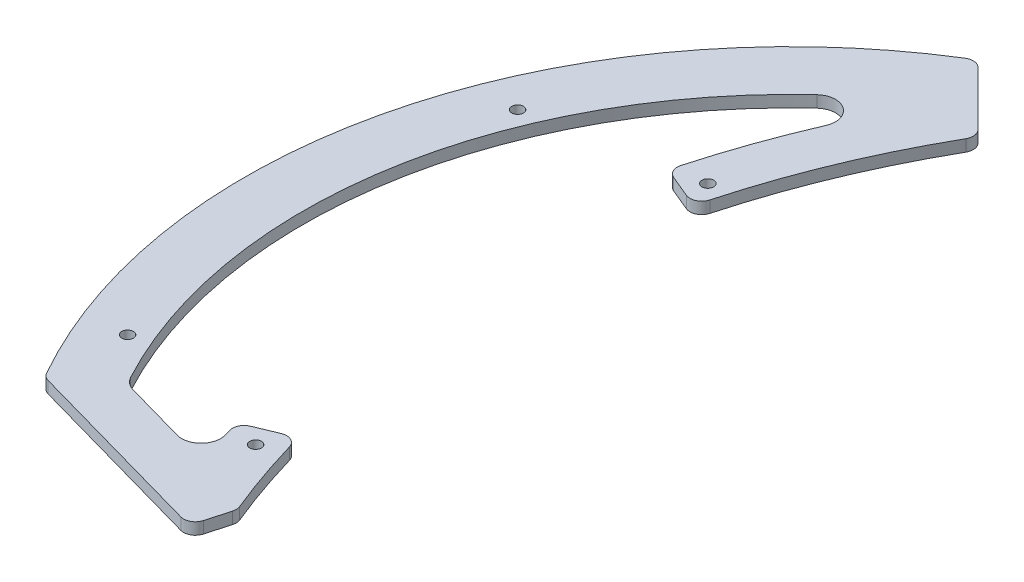
SolidWorks part; units mm, degrees
material "1060 Alloy"
ref_plane "Front Plane" through (0, 0, 0) normal (0, 0, 1) x (1, 0, 0)
ref_plane "Top Plane" through (0, 0, 0) normal (0, 1, 0) x (1, 0, 0)
ref_plane "Right Plane" through (0, 0, 0) normal (1, 0, 0) x (0, 0, -1)
sketch "Sketch1" plane through (0, 0, 0) normal (0, 1, 0) x (1, 0, 0)
  circle A0 centre (0, 0) radius 140
  dimension "D1" = 280
extrude "Boss-Extrude1" add sketch "Sketch1" along normal blind 3
sketch "Sketch17" plane through (0, 0, 0) normal (0, -1, 0) x (1, 0, 0)
  line L0 (-50, 90) -> (-121.2436, 70)
  line L1 (-50, 90) -> (50, 90)
  line L2 (-121.2436, 70) -> (-121.2436, 140)
  line L3 (-121.2436, 140) -> (121.2436, 140)
  line L4 (121.2436, 140) -> (121.2436, 70)
  line L5 (121.2436, 70) -> (50, 90)
  circle A0 centre (0, 0) radius 140 construction
  dimension "D1" = 90
  dimension "D2" = 50
  dimension "D3" = 50
  dimension "D4" = 70
extrude "Cut-Extrude1" cut sketch "Sketch17" against normal up to next
sketch "Sketch19" plane through (0, 3, 0) normal (0, 1, 0) x (1, 0, 0)
  line L0 (-68.5894, 68.5894) -> (68.5894, -68.5894) construction
  line L1 (97, 40.1787) -> (40.1787, 97) construction
  line L2 (40.1787, 97) -> (-40.1787, 97) construction
  line L3 (-40.1787, 97) -> (-97, 40.1787) construction
  line L4 (-97, 40.1787) -> (-97, -40.1787) construction
  line L5 (-97, -40.1787) -> (-40.1787, -97) construction
  line L6 (-40.1787, -97) -> (40.1787, -97) construction
  line L7 (40.1787, -97) -> (97, -40.1787) construction
  line L8 (97, -40.1787) -> (97, 40.1787) construction
  line L9 (68.5894, 68.5894) -> (-68.5894, -68.5894) construction
  circle A0 centre (-79.196, -57.9828) radius 1.5
  circle A1 centre (-79.196, 57.9828) radius 1.5
  circle A2 centre (79.196, 57.9828) radius 1.5
  circle A3 centre (79.196, -57.9828) radius 1.5
  circle A4 centre (0, 0) radius 97 construction
  circle A5 centre (-57.9828, 79.196) radius 1.5
  circle A6 centre (57.9828, 79.196) radius 1.5
  circle A7 centre (57.9828, -79.196) radius 1.5
  circle A8 centre (-57.9828, -79.196) radius 1.5
  dimension "D5" = 3
  dimension "D1" = 15
  dimension "D6" = 97
extrude "Cut-Extrude3" cut sketch "Sketch19" against normal up to next
sketch "Sketch25" plane through (0, 3, 0) normal (0, 1, 0) x (1, 0, 0)
  circle A0 centre (-120, 50) radius 1.5
  circle A1 centre (-120, -50) radius 1.5
  dimension "D1" = 3
  dimension "D2" = 50
  dimension "D3" = 50
  dimension "D4" = 120
extrude "Cut-Extrude10" cut sketch "Sketch25" against normal up to next
sketch "Sketch20" plane through (0, 3, 0) normal (0, 1, 0) x (1, 0, 0)
  line L0 (-72, 120.0666) -> (-50, 98.0666)
  line L1 (-50, 98.0666) -> (50, 98.0666)
  line L2 (50, 98.0666) -> (72, 120.0666)
  arc A1 (121.2436, -70) -> (-121.2436, -70) centre (0, 0) ccw construction
  dimension "D1" = 144
  dimension "D2" = 100
  dimension "D3" = 50
extrude "Cut-Extrude4" cut sketch "Sketch20" against normal up to next
fillet "Fillet2" radius 10 2 edges at (50, 1.5, -98.0666) (-50, 1.5, -98.0666)
sketch "Sketch23" plane through (0, 3, 0) normal (0, 1, 0) x (1, 0, 0)
  line L0 (-67.1106, -74.7122) -> (-73.1897, -96.3671)
  line L1 (-72, 120.0666) -> (-52.9289, 100.9956) construction
  line L2 (-121.2436, -70) -> (-50, -90) construction
  arc A0 (-54.9334, 103) -> (-67.1106, -74.7122) centre (117.6332, 1.902) ccw
  arc A3 (-67.1106, -74.7122) -> (-54.9334, -99.196) centre (117.6332, 1.902) ccw construction
  circle A4 centre (-57.9828, -79.196) radius 1.5 construction
  dimension "D1" = 103
  dimension "D2" = 20
  dimension "D3" = 200
  dimension "D4" = 90
  dimension "D5" = 10
extrude "Cut-Extrude8" cut sketch "Sketch23" against normal through all and the other way through all
sketch "Sketch24" plane through (0, 3, 0) normal (0, 1, 0) x (1, 0, 0)
  line L0 (-87.3571, 55.9666) -> (-76.1692, 51.3049)
  line L1 (-109.1428, -60.9331) -> (-82.3519, -68.4541)
  line L3 (-121.2436, -70) -> (-69.8389, -84.4307) construction
  line L4 (-86.4256, -55.5785) -> (-75.2633, -50.9275)
  line L5 (-120, 50) -> (0, 0) construction
  line L6 (0, 0) -> (-120, -50) construction
  line L7 (-76.1692, 51.3049) -> (-75.2633, -50.9275)
  arc A1 (-87.3571, 55.9666) -> (-67.4898, 105.2147) centre (117.6332, 1.902) cw
  arc A2 (-54.9334, 103) -> (-67.1106, -74.7122) centre (117.6332, 1.902) ccw construction
  arc A3 (-67.4898, 105.2147) -> (-109.1428, -60.9331) centre (0, 0) ccw
  circle A4 centre (-120, 50) radius 5 construction
  circle A5 centre (-120, -50) radius 5 construction
  arc A6 (-82.3519, -68.4541) -> (-86.4256, -55.5785) centre (117.6332, 1.902) cw
  circle A8 centre (-79.196, -57.9828) radius 1.5 construction
  circle A9 centre (-79.196, 57.9828) radius 1.5 construction
  dimension "D2" = 10
  dimension "D3" = 5
  dimension "D4" = 12
  dimension "D5" = 12
  dimension "D1" = 5
  dimension "D6" = 12
extrude "Cut-Extrude9" cut sketch "Sketch24" against normal up to next
fillet "Fillet4" radius 5 3 edges at (-82.3519, 1.5, 68.4541) (-109.1428, 1.5, 60.9331) (-67.4898, 1.5, -105.2147)
fillet "Fillet5" radius 3 9 edges at (-72, 1.5, -120.0666) (-67.1106, 1.5, 74.7122) (-69.8389, 1.5, 84.4307) (-121.2436, 1.5, 70) (-54.9334, 1.5, -103) (-86.4256, 1.5, 55.5785) (-75.2633, 1.5, 50.9275) (-87.3571, 1.5, -55.9666) (-76.1692, 1.5, -51.3049)
equation "\"D3@Sketch20\" = \"D2@Sketch20\" / 2"
